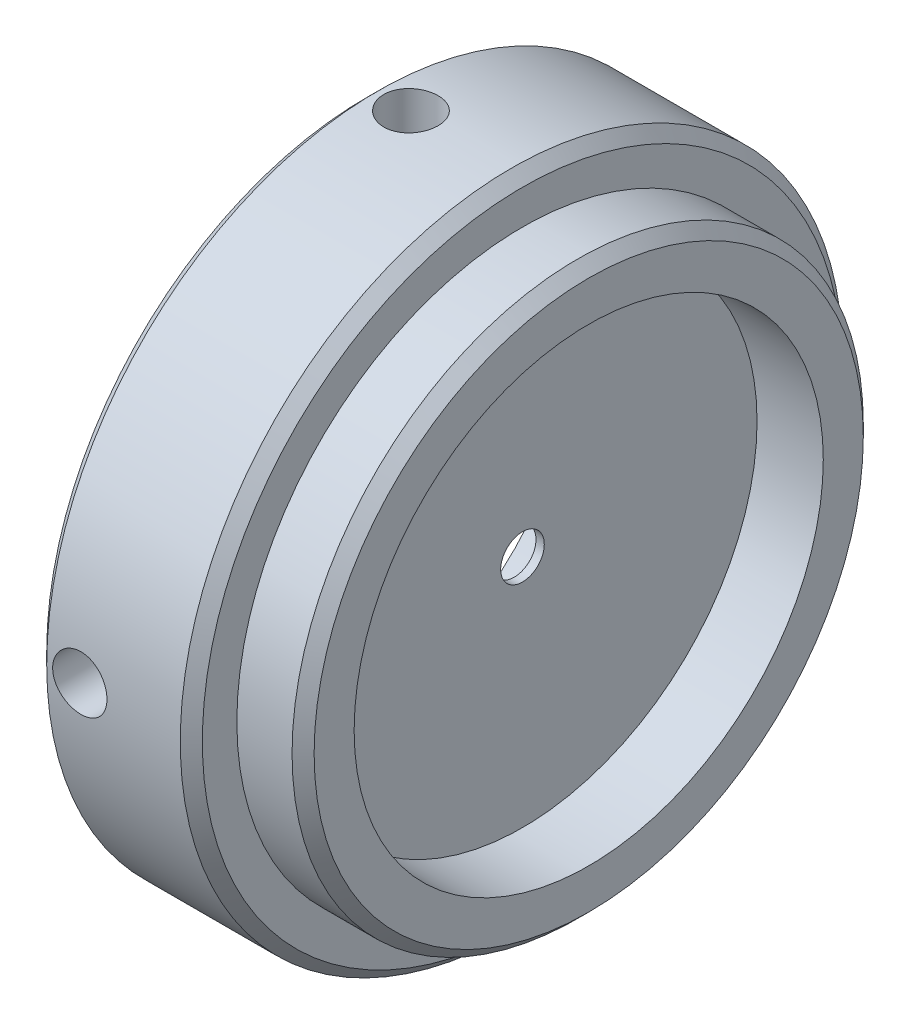
SolidWorks part; units mm, degrees
material "6061-T6 Al"
ref_plane "Front" through (0, 0, 0) normal (0, 0, 1) x (1, 0, 0)
ref_plane "Top" through (0, 0, 0) normal (0, 1, 0) x (1, 0, 0)
ref_plane "Right" through (0, 0, 0) normal (1, 0, 0) x (0, 0, -1)
sketch "Sketch1" plane through (0, 0, 0) normal (0, 0, 1) x (1, 0, 0)
  line L2 (-0.381, 1.0033) -> (-3.0988, 5.7107)
  line L3 (-3.0988, 5.7107) -> (-3.0988, 9.525)
  line L4 (-3.0988, 9.525) -> (-7.1628, 9.525)
  line L5 (-7.1628, 9.525) -> (-7.1628, 15.24)
  line L6 (-7.1628, 15.24) -> (0, 15.24)
  line L7 (0, 15.24) -> (0, 13.1445)
  line L8 (0, 13.1445) -> (3.048, 13.1445)
  line L9 (3.048, 13.1445) -> (3.048, 10.795)
  line L10 (3.048, 10.795) -> (0, 10.795)
  line L11 (0, 10.795) -> (0, 1.0033)
  line L12 (0, 1.0033) -> (-0.381, 1.0033)
  line L13 (0, 0) -> (-25.3401, 0) construction
  dimension "D1" = 2.0066
  dimension "D2" = 0.381
  dimension "D3" = 19.05
  dimension "D4" = 4.064
  dimension "D5" = 7.1628
  dimension "D6" = 60
  dimension "D7" = 30.48
  dimension "D8" = 21.59
  dimension "D9" = 3.048
  dimension "D10" = 26.289
revolve "Revolve1" add sketch "Sketch1" angle 360 about L13
hole_wizard "M3x0.5 Tapped Hole1" positions "3DSketch1" profile "Sketch2" tap size "M3x0.5" standard "ANSI Metric"
sketch3d "3DSketch1"
  line L0 (-5.1308, 15.24, 0) -> (-5.1308, 0, 15.24)
  point P0 (-5.1308, 15.24, 0)
  point P5 (-5.1308, 0, 15.24)
  dimension "D1" = 2.032
sketch "Sketch2" plane through (-5.1308, 15.24, 0) normal (1, 0, 0) x (0, 0, 1)
  line L0 (0, 0) -> (0, 5.715)
  line L1 (0, 5.715) -> (1.25, 5.715)
  line L2 (1.25, 5.715) -> (1.25, 0)
  line L5 (1.25, 0) -> (0, 0)
  line L11 (0, -6.35) -> (0, 107.95) construction
  dimension "Thread Major Dia." = 2.5
  dimension "Thru Tap Drill Depth" = 5.715
chamfer "Chamfer1" distance 0.508 angle 45 3 edges at (3.048, 0, -13.1445) (0, 0, -15.24) (-7.1628, 0, -15.24)
sketch "Sketch3" [suppressed] plane through (0, 0, 0) normal (1, 0, 0) x (0, 0, -1)
  circle A0 centre (0, 0) radius 1.7272
  dimension "D1" = 3.4544
extrude "Cut-Extrude1" [suppressed] cut sketch "Sketch3" against normal through all
